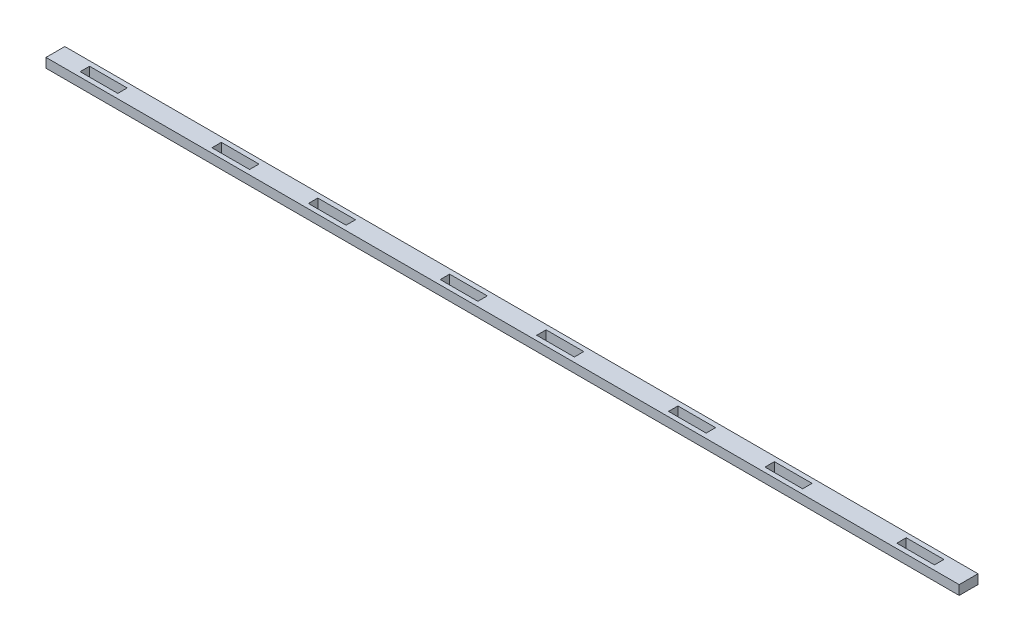
SolidWorks part; units mm, degrees
material "Cedar"
ref_plane "Front Plane" through (0, 0, 0) normal (0, 0, 1) x (1, 0, 0)
ref_plane "Top Plane" through (0, 0, 0) normal (0, 1, 0) x (1, 0, 0)
ref_plane "Right Plane" through (0, 0, 0) normal (1, 0, 0) x (0, 0, -1)
sketch "Sketch1" plane through (0, 0, 0) normal (0, 1, 0) x (1, 0, 0)
  line L1 (-307.9586, 6.35) -> (307.9586, 6.35)
  line L2 (-307.9586, 6.35) -> (-307.9586, -6.35)
  line L3 (-307.9586, -6.35) -> (307.9586, -6.35)
  line L4 (307.9586, 6.35) -> (307.9586, -6.35)
  line L5 (-307.9586, 6.35) -> (307.9586, -6.35) construction
  line L6 (-307.9586, -6.35) -> (307.9586, 6.35) construction
  point P0 (0, 0)
  dimension "D1" = 615.9173
  dimension "D2" = 12.7
extrude "Boss-Extrude1" add sketch "Sketch1" along normal blind 6.35
sketch "Sketch2" plane through (0, 6.35, 0) normal (0, 1, 0) x (1, 0, 0)
  line L0 (-32.5397, 0) -> (32.5397, 0) construction
  line L1 (-45.2397, 3.175) -> (-19.8397, 3.175)
  line L2 (-45.2397, 3.175) -> (-45.2397, -3.175)
  line L3 (-45.2397, -3.175) -> (-19.8397, -3.175)
  line L4 (-19.8397, 3.175) -> (-19.8397, -3.175)
  line L5 (-45.2397, 3.175) -> (-19.8397, -3.175) construction
  line L6 (-45.2397, -3.175) -> (-19.8397, 3.175) construction
  line L7 (19.8397, 3.175) -> (45.2397, 3.175)
  line L8 (19.8397, 3.175) -> (19.8397, -3.175)
  line L9 (19.8397, -3.175) -> (45.2397, -3.175)
  line L10 (45.2397, 3.175) -> (45.2397, -3.175)
  line L11 (19.8397, 3.175) -> (45.2397, -3.175) construction
  line L12 (19.8397, -3.175) -> (45.2397, 3.175) construction
  line L13 (-108.7397, 0) -> (-45.2397, 0) construction
  line L14 (-134.1397, 3.175) -> (-108.7397, 3.175)
  line L15 (-134.1397, 3.175) -> (-134.1397, -3.175)
  line L16 (-134.1397, -3.175) -> (-108.7397, -3.175)
  line L17 (-108.7397, 3.175) -> (-108.7397, -3.175)
  line L18 (-134.1397, 3.175) -> (-108.7397, -3.175) construction
  line L19 (-134.1397, -3.175) -> (-108.7397, 3.175) construction
  line L20 (108.7397, 3.175) -> (134.1397, 3.175)
  line L21 (108.7397, 3.175) -> (108.7397, -3.175)
  line L22 (108.7397, -3.175) -> (134.1397, -3.175)
  line L23 (134.1397, 3.175) -> (134.1397, -3.175)
  line L24 (108.7397, 3.175) -> (134.1397, -3.175) construction
  line L25 (108.7397, -3.175) -> (134.1397, 3.175) construction
  line L26 (45.2397, 0) -> (108.7397, 0) construction
  point P0 (-32.5397, 0)
  point P5 (32.5397, 0)
  point P12 (0, 0)
  point P13 (121.4397, 0)
  point P16 (-121.4397, 0)
  dimension "D1" = 65.0793
  dimension "D2" = 25.4
  dimension "D3" = 25.4
  dimension "D4" = 6.35
  dimension "D5" = 6.35
  dimension "D6" = 6.35
  dimension "D7" = 25.4
  dimension "D8" = 63.5
  dimension "D9" = 25.4
  dimension "D10" = 6.35
  dimension "D11" = 63.5
extrude "Cut-Extrude1" cut sketch "Sketch2" against normal through all
pattern_linear "LPattern1" count 2 spacing 307.9586 along (1, 0, 0) count 2 spacing 307.9586 along (-1, 0, 0) of "Cut-Extrude1"
